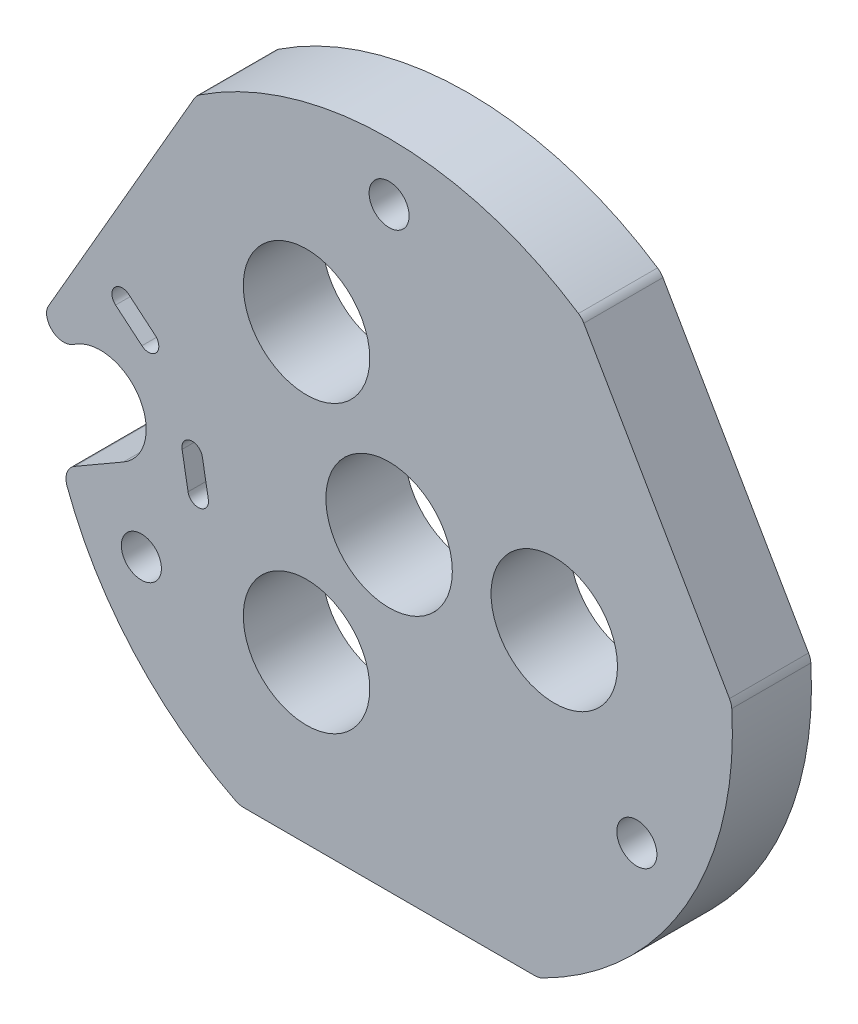
SolidWorks part; units mm, degrees
ref_plane "Front Plane" through (0, 0, 0) normal (0, 0, 1) x (1, 0, 0)
ref_plane "Top Plane" through (0, 0, 0) normal (0, 1, 0) x (1, 0, 0)
ref_plane "Right Plane" through (0, 0, 0) normal (1, 0, 0) x (0, 0, -1)
sketch "Sketch1" plane through (0, 0, 0) normal (0, 0, 1) x (1, 0, 0)
  line L0 (24.6892, 41.401) -> (24.1683, 44.3554)
  line L1 (22.3956, 44.0429) -> (22.9166, 41.0884)
  line L2 (20.0402, 51.5055) -> (17.742, 53.4339)
  line L3 (16.585, 52.055) -> (18.8832, 50.1267)
  line L4 (27.7592, 19.6183) -> (53.2151, 19.6183)
  line L5 (70.2338, 49.0956) -> (57.5059, 71.141)
  line L6 (23.4684, 71.141) -> (10.7323, 49.0813)
  line L7 (12.7977, 47.1761) -> (13.2607, 47.4435)
  line L8 (17.2607, 40.5153) -> (12.9982, 38.0543)
  circle A0 centre (33.2703, 34.1183) radius 5.525
  circle A1 centre (54.9209, 46.6183) radius 5.525
  circle A2 centre (33.2703, 59.1183) radius 5.525
  circle A3 centre (40.4871, 46.6183) radius 5.525
  circle A4 centre (18.8365, 34.1183) radius 1.75
  circle A5 centre (62.1378, 34.1183) radius 1.75
  circle A6 centre (40.4871, 71.6183) radius 1.75
  arc A7 (22.9166, 41.0884) -> (24.6892, 41.401) centre (23.8029, 41.2447) ccw
  arc A8 (24.1683, 44.3554) -> (22.3956, 44.0429) centre (23.282, 44.1991) ccw
  arc A9 (18.8832, 50.1267) -> (20.0402, 51.5055) centre (19.4617, 50.8161) ccw
  arc A10 (17.742, 53.4339) -> (16.585, 52.055) centre (17.1635, 52.7445) ccw
  arc A11 (12.9982, 38.0543) -> (12.3409, 36.2362) centre (13.7482, 36.7553) ccw
  arc A12 (12.3409, 36.2362) -> (27.0893, 19.7762) centre (40.4871, 46.6183) ccw
  arc A13 (27.0893, 19.7762) -> (27.7592, 19.6183) centre (27.7592, 21.1183) ccw
  arc A14 (53.2151, 19.6183) -> (53.8849, 19.7762) centre (53.2151, 21.1183) ccw
  arc A15 (53.8849, 19.7762) -> (70.432, 48.4365) centre (40.4871, 46.6183) ccw
  arc A16 (70.432, 48.4365) -> (70.2338, 49.0956) centre (68.9347, 48.3456) ccw
  arc A17 (57.5059, 71.141) -> (57.0342, 71.6422) centre (56.2068, 70.391) ccw
  arc A18 (57.0342, 71.6422) -> (23.9401, 71.6422) centre (40.4871, 46.6183) ccw
  arc A19 (23.9401, 71.6422) -> (23.4684, 71.141) centre (24.7674, 70.391) ccw
  arc A20 (10.7323, 49.0813) -> (10.5509, 48.5729) centre (12.0313, 48.3313) ccw
  arc A21 (10.5509, 48.5729) -> (12.7977, 47.1761) centre (12.0477, 48.4752) ccw
  arc A22 (17.2607, 40.5153) -> (13.2607, 47.4435) centre (15.2607, 43.9794) ccw
extrude "Boss-Extrude1" add sketch "Sketch1" along normal blind 6.91
